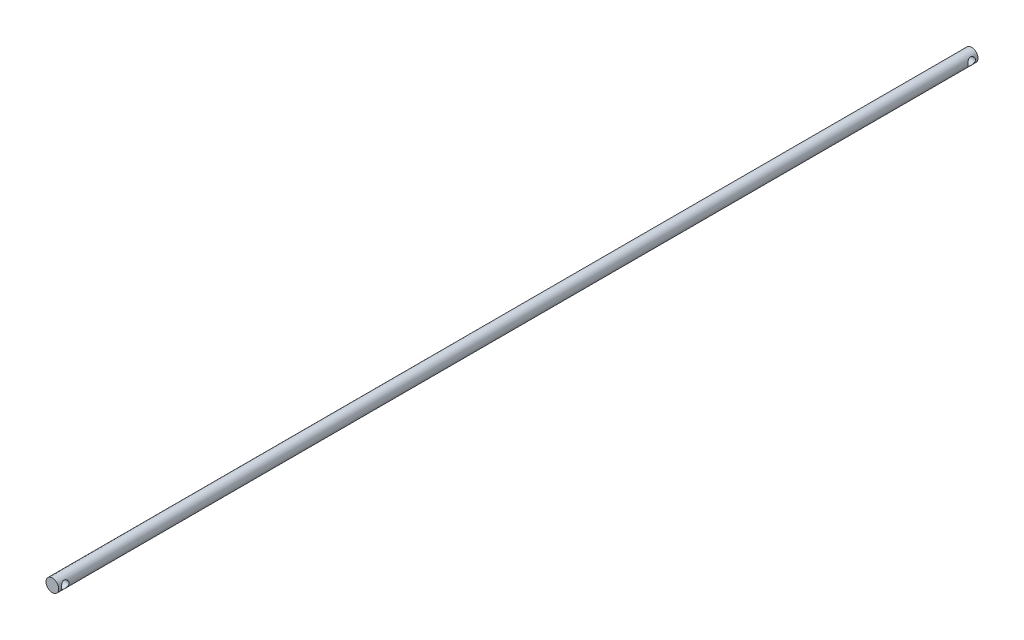
SolidWorks part; units mm, degrees
ref_plane "Front Plane" through (0, 0, 0) normal (0, 0, 1) x (1, 0, 0)
ref_plane "Top Plane" through (0, 0, 0) normal (0, 1, 0) x (1, 0, 0)
ref_plane "Right Plane" through (0, 0, 0) normal (1, 0, 0) x (0, 0, -1)
sketch "Sketch2" plane through (0, 0, 0) normal (0, 0, 1) x (1, 0, 0)
  circle A0 centre (0, 0) radius 2.5
  dimension "D1" = 5
extrude "Boss-Extrude1" add sketch "Sketch2" along normal blind 360
sketch "Sketch3" plane through (0, 0, 0) normal (1, 0, 0) x (0, 0, -1)
  line L0 (-360, 2.5) -> (-360, -2.5) construction
  line L1 (-360, -2.5) -> (-354.8705, -2.5) construction
  line L2 (-360, -2.5) -> (0, -2.5) construction
  line L3 (-354.8705, -2.5) -> (-360, 2.5) construction
  line L4 (-360, 2.5) -> (-354.8705, 2.5) construction
  line L5 (0, 2.5) -> (-360, 2.5) construction
  line L6 (-354.8705, 2.5) -> (-360, -2.5) construction
  line L7 (0, 2.5) -> (0, -2.5) construction
  line L8 (0, -2.5) -> (-4.9913, -2.5) construction
  line L9 (-4.9913, -2.5) -> (0, 2.5) construction
  line L10 (0, 2.5) -> (-4.9913, 2.5) construction
  line L11 (-4.9913, 2.5) -> (0, -2.5) construction
  circle A0 centre (-357.4353, 0) radius 1.5
  circle A1 centre (-2.4956, 0) radius 1.5
  dimension "D1" = 3
  dimension "D2" = 3
extrude "Cut-Extrude1" cut sketch "Sketch3" against normal through all and the other way through all
